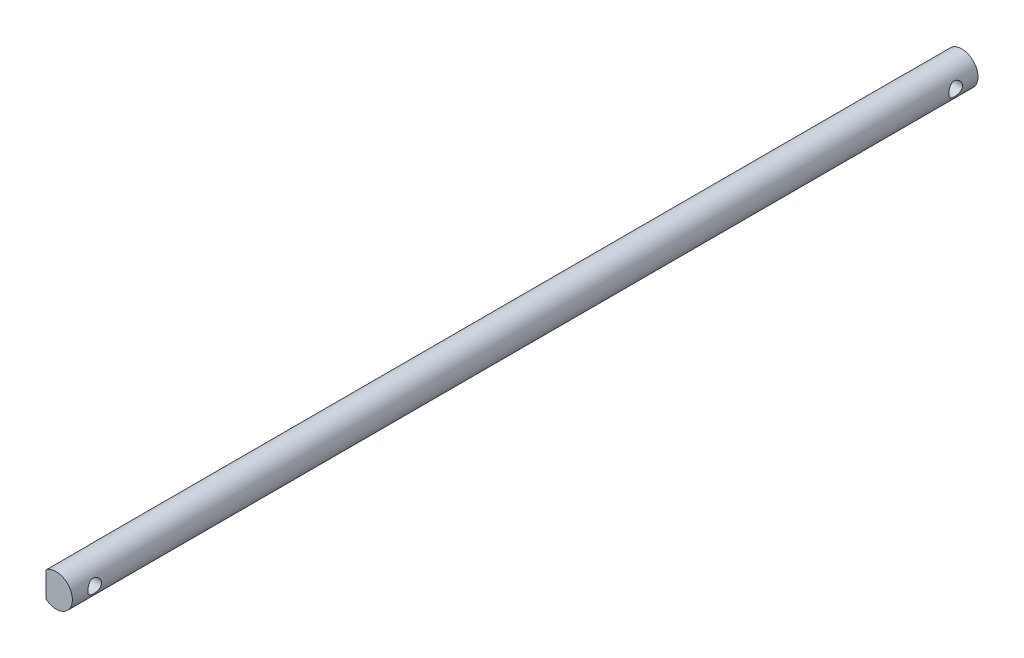
SolidWorks part; units mm, degrees
material "AISI 1015 Acero estirado en frío (SS)"
ref_plane "Alzado" through (0, 0, 0) normal (0, 0, 1) x (1, 0, 0)
ref_plane "Planta" through (0, 0, 0) normal (0, 1, 0) x (1, 0, 0)
ref_plane "Vista lateral" through (0, 0, 0) normal (1, 0, 0) x (0, 0, -1)
sketch "Croquis1" plane through (0, 0, 0) normal (0, 0, 1) x (1, 0, 0)
  circle A0 centre (0, 0) radius 4
  dimension "D1" = 8
extrude "Saliente-Extruir1" add sketch "Croquis1" along normal blind 223
sketch "Croquis2" plane through (0, 0, 223) normal (0, 0, 1) x (1, 0, 0)
  line L0 (-2.5, 3.1225) -> (-2.5, -3.1225)
  circle A1 centre (0, 0) radius 4
  circle A2 centre (0, 0) radius 4
  circle M3 centre (0, 0) radius 4
  dimension "D2" = 2.5
  dimension "D1" = 0
extrude "Cortar-Extruir1" cut sketch "Croquis2" against normal blind 11 contours L0 M3
ref_plane "Plano1" through (0, 0, 111.5) normal (0, 0, 1) x (1, 0, 0)
mirror "Simetría1" about plane through (0, 0, 111.5) normal (0, 0, 1) of "Cortar-Extruir1"
sketch "Croquis3" plane through (-2.5, 0, 0) normal (-1, 0, 0) x (0, 0, 1)
  line L0 (212, 3.1225) -> (223, 3.1225) construction
  line L1 (223, 3.1225) -> (223, -3.1225) construction
  circle A0 centre (217.5, 0) radius 1.5875
  point P5 (217.5, 3.1225)
  point P8 (223, 0)
  dimension "D1" = 3.175
hole_wizard "Taladro de margen para M31" positions "Croquis3D3" profile "Croquis6" hole size "M3" standard "ISO" end condition through all
sketch3d "Croquis3D3"
  point P0 (-2.5, 0, 217.5)
sketch "Croquis6" plane through (-2.5, 0, 217.5) normal (0, 1, 0) x (0, 0, 1)
  line L0 (0, 0) -> (0, 6.5)
  line L1 (0, 6.5) -> (1.7, 6.5)
  line L2 (1.7, 6.5) -> (1.7, 0)
  line L5 (1.7, 0) -> (0, 0)
  line L11 (0, -6.35) -> (0, 107.95) construction
  dimension "Diámetro de taladro hasta el siguiente" = 3.4
  dimension "Profundidad de taladro hasta el siguiente" = 6.5
mirror "Simetría3" about plane through (0, 0, 111.5) normal (0, 0, 1) of "Taladro de margen para M31"
